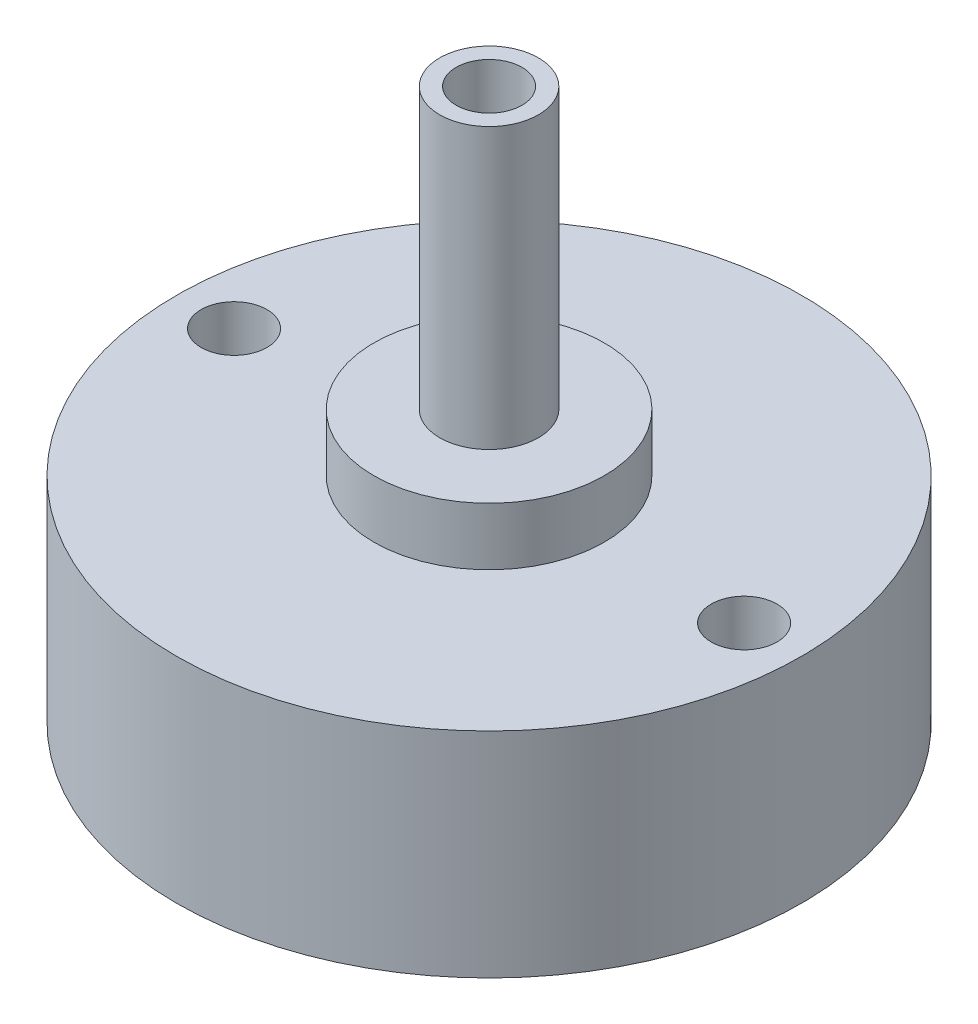
SolidWorks part; units mm, degrees
ref_plane "Ön Düzlem" through (0, 0, 0) normal (0, 0, 1) x (1, 0, 0)
ref_plane "Üst Düzlem" through (0, 0, 0) normal (0, 1, 0) x (1, 0, 0)
ref_plane "Sağ Düzlem" through (0, 0, 0) normal (1, 0, 0) x (0, 0, -1)
sketch "Çizim1" plane through (0, 0, 0) normal (0, 1, 0) x (1, 0, 0)
  circle A0 centre (0, 0) radius 19
  dimension "D1" = 38
extrude "Yükseklik-Ekstrüzyon1" add sketch "Çizim1" against normal blind 13
sketch "Çizim2" plane through (0, 0, 0) normal (0, 1, 0) x (1, 0, 0)
  circle A0 centre (-15.5, 0) radius 2
  circle A1 centre (15.5, 0) radius 2
  dimension "D1" = 31
  dimension "D2" = 15.5
  dimension "D3" = 4
extrude "Kes-Ekstrüzyon1" cut sketch "Çizim2" against normal blind 10
sketch "Çizim3" plane through (0, 0, 0) normal (0, 1, 0) x (1, 0, 0)
  circle A0 centre (0, 0) radius 7
  dimension "D1" = 14
extrude "Yükseklik-Ekstrüzyon2" add sketch "Çizim3" along normal blind 3.5
sketch "Çizim4" plane through (0, 3.5, 0) normal (0, 1, 0) x (1, 0, 0)
  circle A0 centre (0, 0) radius 3
  circle A1 centre (0, 0) radius 2
  dimension "D1" = 6
  dimension "D2" = 4
extrude "Yükseklik-Ekstrüzyon3" add sketch "Çizim4" along normal blind 17
